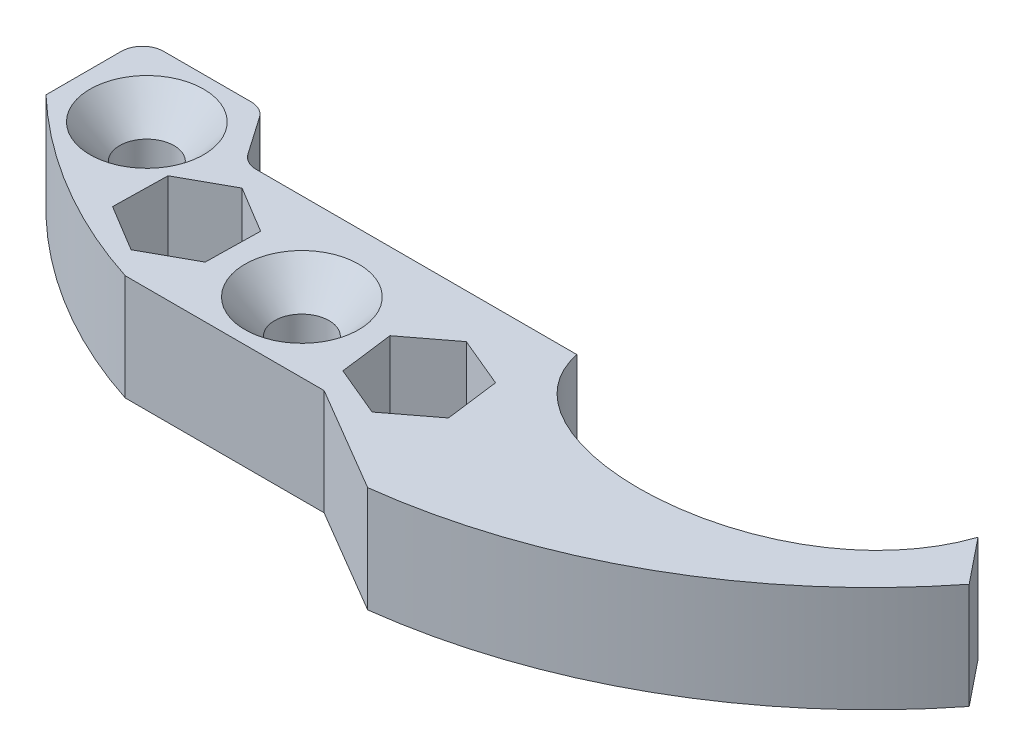
SolidWorks part; units mm, degrees
material "PE High Density"
ref_plane "Front Plane" through (0, 0, 0) normal (0, 0, 1) x (1, 0, 0)
ref_plane "Top Plane" through (0, 0, 0) normal (0, 1, 0) x (1, 0, 0)
ref_plane "Right Plane" through (0, 0, 0) normal (1, 0, 0) x (0, 0, -1)
sketch "Sketch1" plane through (0, 0, 0) normal (0, 1, 0) x (1, 0, 0)
  line L0 (-8.8733, 0) -> (29.5955, 0)
  line L2 (45.2043, 0) -> (-8.8733, 0) construction
  line L3 (29.5955, 0) -> (45.2043, 0) construction
  line L4 (72.6275, 5.0746) -> (76.9724, -0.3288)
  line L7 (30.8655, -26.3694) -> (18.1655, -18.896)
  line L8 (18.1655, -18.896) -> (-5.6888, -18.896)
  line L9 (-29.2338, -4.8553) -> (-29.2338, 4.1773)
  line L10 (-26.6938, 6.7173) -> (-16.1913, 6.7173)
  line L11 (-14.1042, 5.6249) -> (-10.9603, 1.0924)
  arc A0 (-8.8733, 0) -> (-10.9603, 1.0924) centre (-8.8733, 2.54) cw
  circle A1 centre (-20.3688, -1.6242) radius 3.2639
  circle A2 centre (-7.9084, -9.3171) radius 3.2639
  circle A3 centre (7.107, -10.5038) radius 3.2639
  circle A4 centre (22.4448, -11.7675) radius 3.2639
  arc A7 (-16.1913, 6.7173) -> (-14.1042, 5.6249) centre (-16.1913, 4.1773) cw
  arc A8 (-26.6938, 6.7173) -> (-29.2338, 4.1773) centre (-26.6938, 4.1773) ccw
  arc A9 (-29.2338, -4.8553) -> (-5.6888, -18.896) centre (13.2373, 39.6028) ccw
  arc A10 (30.8655, -26.3694) -> (76.9724, -0.3288) centre (22.2088, 42.7962) ccw
  spline S0 degree 3 poles (29.5955, 0) (32.608, -14.845) (66.1768, -13.6989) (72.6275, 5.0746) knots 0 0 0 0 1 1 1 1
  dimension "D1" = 6.5278
extrude "Boss-Extrude1" add sketch "Sketch1" along normal blind 12.7
chamfer "Chamfer1" distance 4.0894 angle 41 2 edges at (7.107, 12.7, 13.7677) (-20.3688, 12.7, 4.8881)
sketch "Sketch2" plane through (0, 12.7, 0) normal (0, 1, 0) x (1, 0, 0)
  line L1 (-2.1916, -6.1549) -> (-7.7886, -2.7851)
  line L2 (-7.7886, -2.7851) -> (-13.5054, -5.9474)
  line L3 (-13.5054, -5.9474) -> (-13.6251, -12.4794)
  line L4 (-13.6251, -12.4794) -> (-8.0281, -15.8492)
  line L5 (-8.0281, -15.8492) -> (-2.3113, -12.6869)
  line L6 (-2.3113, -12.6869) -> (-2.1916, -6.1549)
  line L7 (28.4718, -14.2889) -> (27.6419, -7.8087)
  line L8 (27.6419, -7.8087) -> (21.6149, -5.2873)
  line L9 (21.6149, -5.2873) -> (16.4179, -9.2461)
  line L10 (16.4179, -9.2461) -> (17.2478, -15.7263)
  line L11 (17.2478, -15.7263) -> (23.2747, -18.2477)
  line L12 (23.2747, -18.2477) -> (28.4718, -14.2889)
  circle A0 centre (-7.9084, -9.3171) radius 5.6578 construction
  circle A1 centre (22.4448, -11.7675) radius 5.6578 construction
  dimension "D1" = 11.3157
extrude "Cut-Extrude1" cut sketch "Sketch2" against normal through all
